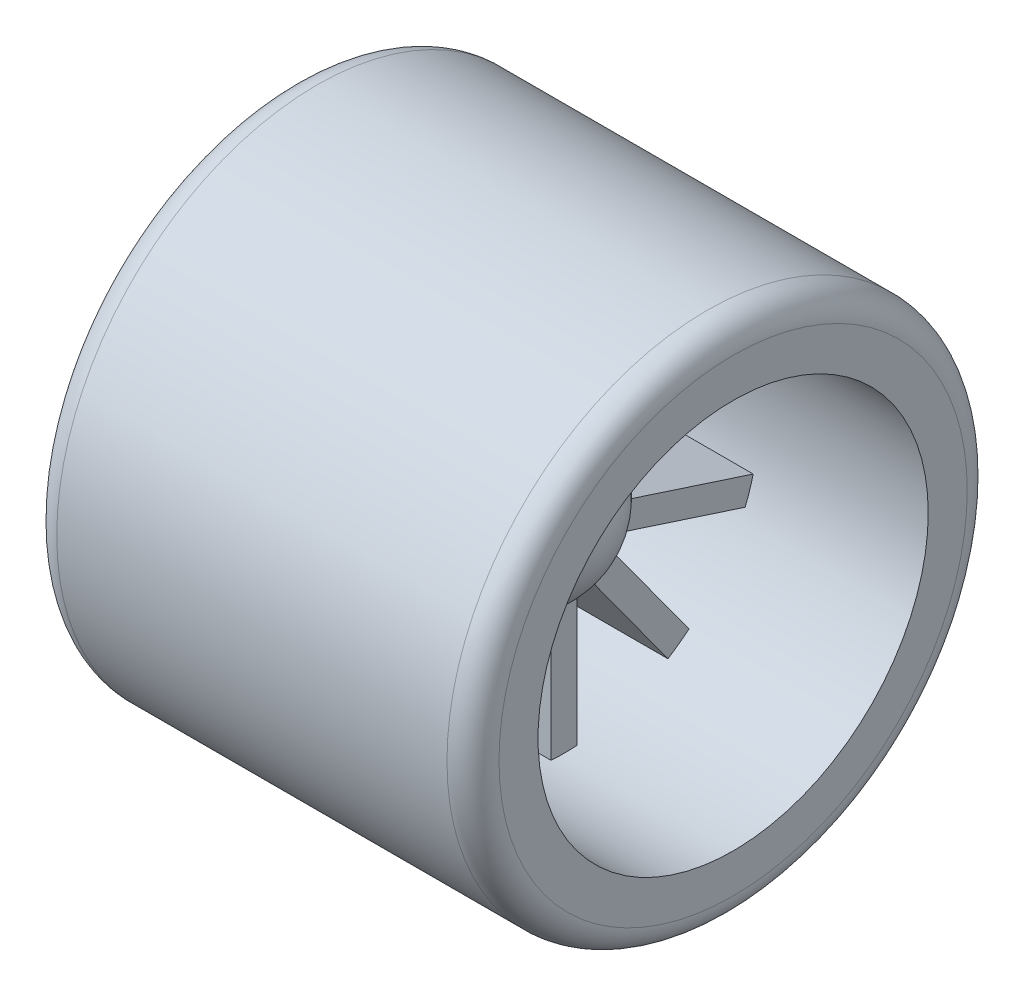
SolidWorks part; units mm, degrees
ref_plane "Front Plane" through (0, 0, 0) normal (0, 0, 1) x (1, 0, 0)
ref_plane "Top Plane" through (0, 0, 0) normal (0, 1, 0) x (1, 0, 0)
ref_plane "Right Plane" through (0, 0, 0) normal (1, 0, 0) x (0, 0, -1)
sketch "Sketch1" plane through (0, 0, 0) normal (1, 0, 0) x (0, 0, -1)
  circle A0 centre (0, 0) radius 25.4
  circle A1 centre (0, 0) radius 19.05
  dimension "D1" = 50.8
  dimension "D2" = 38.1
extrude "Boss-Extrude1" add sketch "Sketch1" along normal mid plane 43.18
fillet "Fillet1" radius 2.54 2 edges at (-21.59, 0, -25.4) (21.59, 0, -25.4)
sketch "Sketch2" plane through (0, 0, 0) normal (1, 0, 0) x (0, 0, -1)
  line L0 (0, 19.05) -> (0, 0) construction
  line L1 (0, 0) -> (19.05, 0) construction
  line L2 (1.27, 22.8247) -> (1.27, 4.9187)
  line L3 (-1.27, 4.9187) -> (-1.27, 22.8247)
  line L4 (-1.27, 22.8247) -> (1.27, 22.8247)
  line L5 (-1.27, 4.9187) -> (1.27, 4.9187)
  line L6 (1.8637, 4.7258) -> (3.9186, 3.2328)
  line L7 (1.8637, 4.7258) -> (12.3886, 19.2121)
  line L8 (14.4435, 17.7191) -> (3.9186, 3.2328)
  line L9 (12.3886, 19.2121) -> (14.4435, 17.7191)
  line L10 (4.2855, 2.7278) -> (5.0704, 0.3121)
  line L11 (4.2855, 2.7278) -> (21.3151, 8.2611)
  line L12 (22.1, 5.8454) -> (5.0704, 0.3121)
  line L13 (21.3151, 8.2611) -> (22.1, 5.8454)
  line L14 (5.0704, -0.3121) -> (4.2855, -2.7278)
  line L15 (5.0704, -0.3121) -> (22.1, -5.8454)
  line L16 (21.3151, -8.2611) -> (4.2855, -2.7278)
  line L17 (22.1, -5.8454) -> (21.3151, -8.2611)
  line L18 (3.9186, -3.2328) -> (1.8637, -4.7258)
  line L19 (3.9186, -3.2328) -> (14.4435, -17.7191)
  line L20 (12.3886, -19.2121) -> (1.8637, -4.7258)
  line L21 (14.4435, -17.7191) -> (12.3886, -19.2121)
  line L22 (1.27, -4.9187) -> (-1.27, -4.9187)
  line L23 (1.27, -4.9187) -> (1.27, -22.8247)
  line L24 (-1.27, -22.8247) -> (-1.27, -4.9187)
  line L25 (1.27, -22.8247) -> (-1.27, -22.8247)
  line L26 (-1.8637, -4.7258) -> (-3.9186, -3.2328)
  line L27 (-1.8637, -4.7258) -> (-12.3886, -19.2121)
  line L28 (-14.4435, -17.7191) -> (-3.9186, -3.2328)
  line L29 (-12.3886, -19.2121) -> (-14.4435, -17.7191)
  line L30 (-4.2855, -2.7278) -> (-5.0704, -0.3121)
  line L31 (-4.2855, -2.7278) -> (-21.3151, -8.2611)
  line L32 (-22.1, -5.8454) -> (-5.0704, -0.3121)
  line L33 (-21.3151, -8.2611) -> (-22.1, -5.8454)
  line L34 (-5.0704, 0.3121) -> (-4.2855, 2.7278)
  line L35 (-5.0704, 0.3121) -> (-22.1, 5.8454)
  line L36 (-21.3151, 8.2611) -> (-4.2855, 2.7278)
  line L37 (-22.1, 5.8454) -> (-21.3151, 8.2611)
  line L38 (-3.9186, 3.2328) -> (-1.8637, 4.7258)
  line L39 (-3.9186, 3.2328) -> (-14.4435, 17.7191)
  line L40 (-12.3886, 19.2121) -> (-1.8637, 4.7258)
  line L41 (-14.4435, 17.7191) -> (-12.3886, 19.2121)
  circle A0 centre (0, 0) radius 19.05 construction
  circle A1 centre (0, 0) radius 22.86 construction
  circle A2 centre (0, 0) radius 5.08 construction
  point P14 (0, 22.8247)
  point P53 (0, 0)
  dimension "D1" = 10.16
  dimension "D2" = 2.54
  dimension "D3" = 10
extrude "Boss-Extrude2" add sketch "Sketch2" along normal mid plane 10.16
sketch "Sketch3" plane through (0, 0, 0) normal (1, 0, 0) x (0, 0, -1)
  line L0 (0, 8.255) -> (0, -8.255)
  arc A0 (0, 8.255) -> (0, -8.255) centre (0, 0) cw
  point P3 (0, 0)
  dimension "D1" = 16.51
revolve "Revolve1" add sketch "Sketch3" angle 360 about L0
